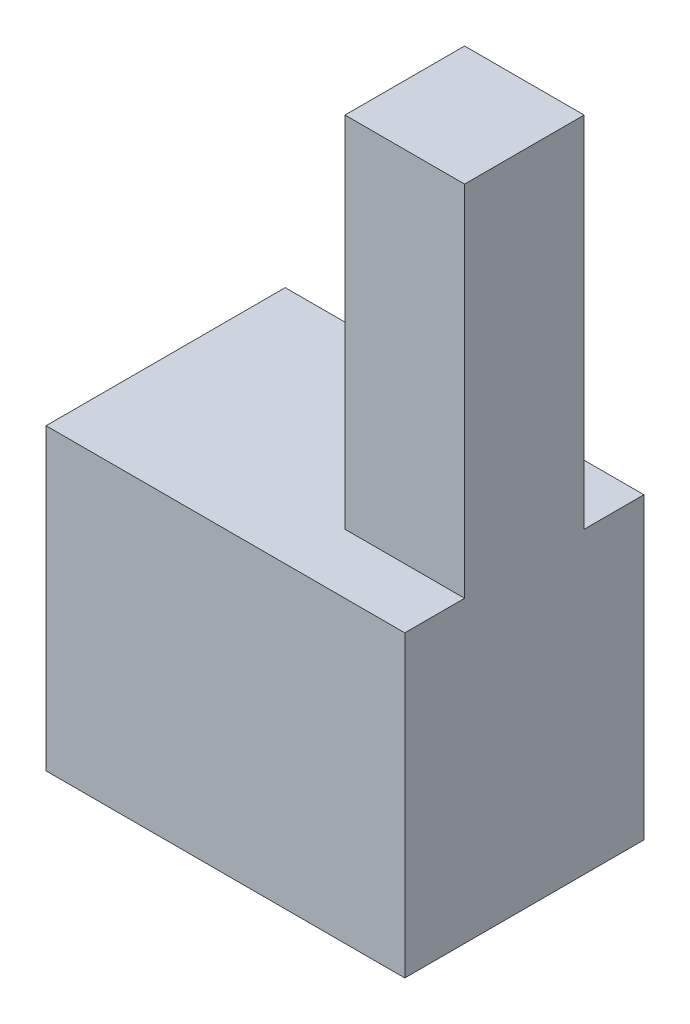
SolidWorks part; units mm, degrees
ref_plane "Front Plane" through (0, 0, 0) normal (0, 0, 1) x (1, 0, 0)
ref_plane "Top Plane" through (0, 0, 0) normal (0, 1, 0) x (1, 0, 0)
ref_plane "Right Plane" through (0, 0, 0) normal (1, 0, 0) x (0, 0, -1)
sketch "Sketch3" plane through (0, 0, 0) normal (0, 0, 1) x (1, 0, 0)
  line L0 (0, 0) -> (0, -5)
  line L1 (0, -5) -> (20, -5)
  line L2 (20, -5) -> (20, -25)
  line L3 (0, 0) -> (20, 0)
  line L4 (20, 0) -> (20, 30)
  line L5 (20, 30) -> (30, 30)
  line L6 (30, 30) -> (30, -25)
  line L7 (30, -25) -> (20, -25)
  dimension "D1" = 20
  dimension "D2" = 20
  dimension "D3" = 20
  dimension "D4" = 5
  dimension "D5" = 10
  dimension "D6" = 55
extrude "Boss-Extrude3" add sketch "Sketch3" along normal blind 10
sketch "Sketch5" plane through (0, 0, 10) normal (0, 0, 1) x (1, 0, 0)
  line L5 (0, 0) -> (30, 0)
  line L6 (0, 0) -> (0, -25)
  line L7 (0, -25) -> (30, -25)
  line L8 (30, 0) -> (30, -25)
extrude "Boss-Extrude5" add sketch "Sketch5" along normal blind 5
sketch "Sketch7" plane through (0, 0, 0) normal (0, 0, -1) x (-1, 0, 0)
  line L0 (-20, 0) -> (-30, 0)
  line L1 (-30, 0) -> (-30, -25)
  line L2 (-30, -25) -> (-20, -25)
  line L3 (-20, -25) -> (-20, -5)
  line L4 (-20, -5) -> (0, -5)
  line L5 (0, -5) -> (0, 0)
  line L6 (0, 0) -> (-20.7589, 0)
  line M8 (0, 0) -> (-20, 0)
  line M11 (-30, 30) -> (-30, -25)
  line M12 (-30, -25) -> (-20, -25)
  line M13 (-20, -25) -> (-20, -5)
  line M14 (-20, -5) -> (0, -5)
  line M15 (0, -5) -> (0, 0)
extrude "Boss-Extrude7" add sketch "Sketch7" along normal blind 5 contours L0 M8 M11 M12 M13 M14 M15
